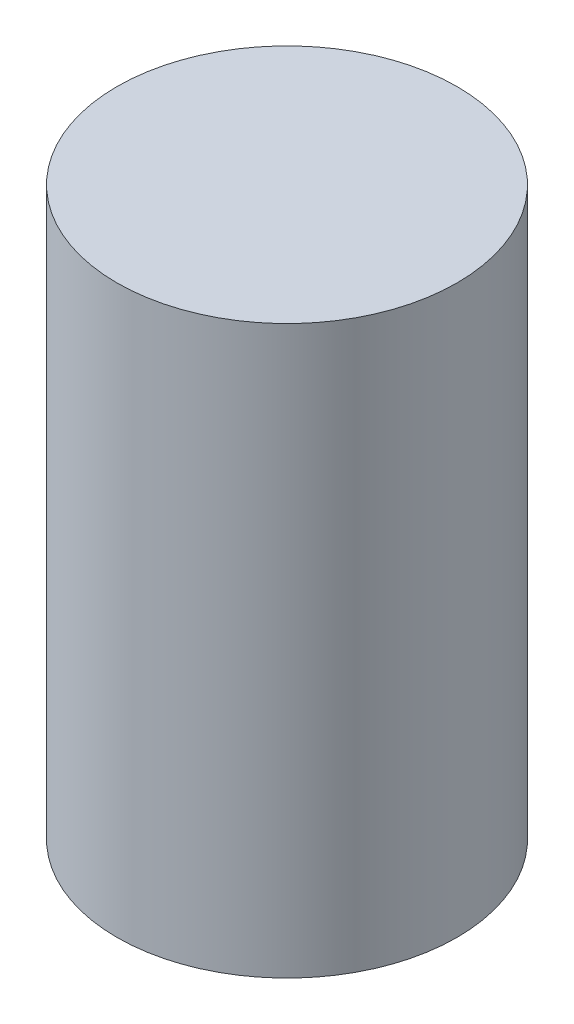
SolidWorks part; units mm, degrees
ref_plane "Plan de face" through (0, 0, 0) normal (0, 0, 1) x (1, 0, 0)
ref_plane "Plan de dessus" through (0, 0, 0) normal (0, 1, 0) x (1, 0, 0)
ref_plane "Plan de droite" through (0, 0, 0) normal (1, 0, 0) x (0, 0, -1)
sketch "Esquisse1" plane through (0, 0, 0) normal (0, 0, 1) x (1, 0, 0)
  line L1 (0, 50) -> (30, 50)
  line L2 (0, 50) -> (0, -50)
  line L3 (0, -50) -> (30, -50)
  line L4 (30, 50) -> (30, -50)
  dimension "D1" = 30
  dimension "D2" = 100
revolve "Révolution1" add sketch "Esquisse1" angle 360 about L2
